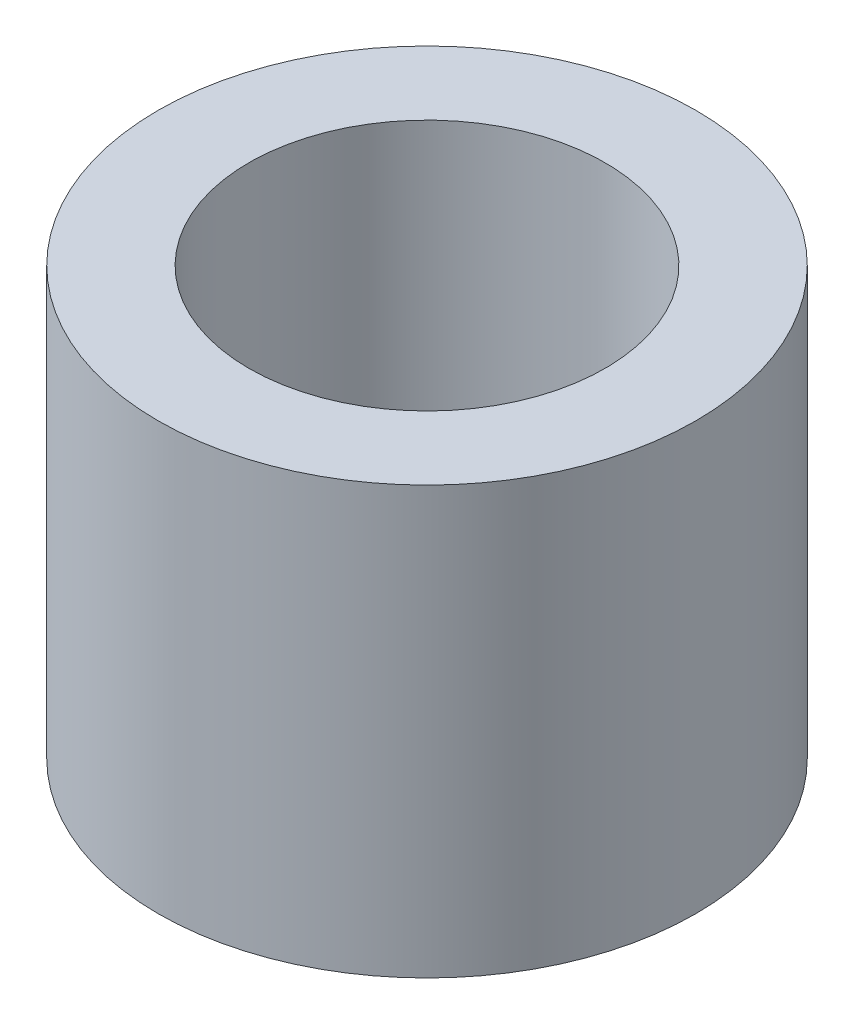
SolidWorks part; units mm, degrees
ref_plane "Alzado" through (0, 0, 0) normal (0, 0, 1) x (1, 0, 0)
ref_plane "Planta" through (0, 0, 0) normal (0, 1, 0) x (1, 0, 0)
ref_plane "Vista lateral" through (0, 0, 0) normal (1, 0, 0) x (0, 0, -1)
sketch "Croquis1" plane through (0, 0, 0) normal (0, 1, 0) x (1, 0, 0)
  circle A0 centre (0, 0) radius 4
  circle A1 centre (0, 0) radius 2.65
  dimension "D1" = 8
  dimension "D2" = 5.3
extrude "Saliente-Extruir1" add sketch "Croquis1" along normal blind 6.35
